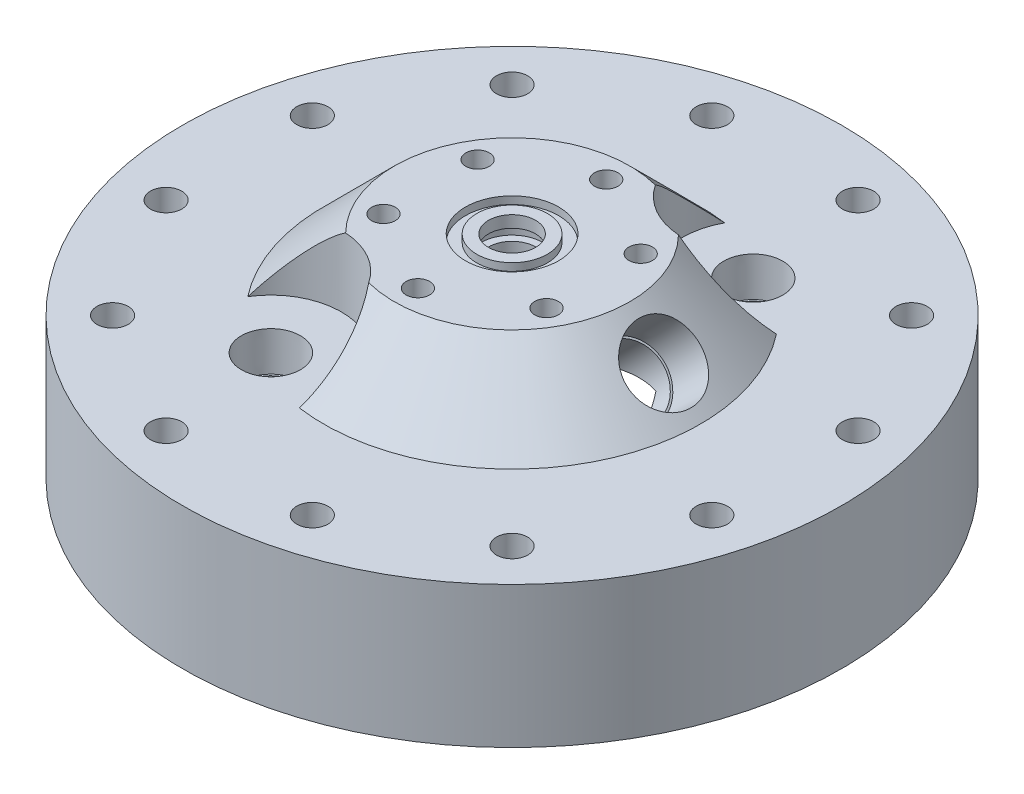
SolidWorks part; units mm, degrees
ref_plane "Front Plane" through (0, 0, 0) normal (0, 0, 1) x (1, 0, 0)
ref_plane "Top Plane" through (0, 0, 0) normal (0, 1, 0) x (1, 0, 0)
ref_plane "Right Plane" through (0, 0, 0) normal (1, 0, 0) x (0, 0, -1)
sketch "Sketch1" plane through (0, 0, 0) normal (0, 0, 1) x (1, 0, 0)
  line L0 (0, 0) -> (0, 51.199) construction
  line L1 (-55.9435, 0) -> (-88.9, 0)
  line L2 (-88.9, 0) -> (-88.9, 38.1)
  line L3 (-88.9, 38.1) -> (-50.8, 38.1)
  line L4 (-50.8, 38.1) -> (-31.75, 57.15)
  line L5 (-31.75, 57.15) -> (-12.573, 57.15)
  line L6 (-6.35, 50.927) -> (-6.35, 31.75)
  line L8 (-31.75, 31.75) -> (-6.35, 31.75)
  line L12 (-31.75, 31.75) -> (-31.75, 19.05)
  line L15 (-31.75, 19.05) -> (-50.8, 19.05)
  line L16 (-50.8, 19.05) -> (-50.8, 0)
  line L17 (-50.8, 0) -> (-52.3875, 0)
  line L18 (-52.3875, 0) -> (-52.3875, 2.54)
  line L19 (-52.3875, 2.54) -> (-55.9435, 2.54)
  line L20 (-55.9435, 2.54) -> (-55.9435, 0)
  line L25 (-6.35, 57.15) -> (-6.35, 53.975)
  line L26 (-6.35, 53.975) -> (-8.382, 53.975)
  line L27 (-8.382, 53.975) -> (-8.382, 50.927)
  line L28 (-8.382, 50.927) -> (-6.35, 50.927)
  line L29 (-12.573, 57.15) -> (-12.573, 55.118)
  line L30 (-12.573, 55.118) -> (-9.525, 55.118)
  line L31 (-9.525, 55.118) -> (-9.525, 57.15)
  line L32 (-9.525, 57.15) -> (-6.35, 57.15)
  dimension "D1" = 6.35
  dimension "D2" = 31.75
  dimension "D3" = 19.05
  dimension "D4" = 25.4
  dimension "D5" = 88.9
  dimension "D6" = 12.7
  dimension "D7" = 135
  dimension "D8" = 6.35
  dimension "D9" = 19.05
  dimension "D10" = 38.1
  dimension "D11" = 3.175
  dimension "D12" = 50.8
  dimension "D13" = 3.556
  dimension "D14" = 2.54
  dimension "D15" = 1.5875
  dimension "D16" = 3.048
  dimension "D17" = 2.032
  dimension "D18" = 3.048
  dimension "D19" = 2.032
  dimension "D20" = 3.175
revolve "Revolve1" add sketch "Sketch1" angle 360 about L0
hole_wizard "5/16 Clearance Hole1" positions "Sketch4" profile "Sketch6" hole size "5/16" standard "ANSI Inch" end condition through all
sketch "Sketch4" plane through (0, 38.1, 0) normal (0, 1, 0) x (1, 0, 0)
  line L0 (-73.6035, -19.722) -> (0, 0) construction
  line L2 (0, 0) -> (-63.9148, 0) construction
  point P0 (-73.6035, -19.722)
  dimension "D1" = 76.2
  dimension "D2" = 15
sketch "Sketch6" plane through (-73.6035, 38.1, 19.722) normal (1, 0, 0) x (0, 0, 1)
  line L0 (0, 0) -> (0, 38.1)
  line L1 (0, 38.1) -> (4.2164, 38.1)
  line L2 (4.2164, 38.1) -> (4.2164, 0)
  line L5 (4.2164, 0) -> (0, 0)
  line L11 (0, -6.35) -> (0, 107.95) construction
  dimension "Thru Hole Dia." = 8.4328
  dimension "Thru Hole Depth" = 38.1
pattern_circular "CirPattern1" count 12 over 360 about axis through (0, 0, 0) along (0, 1, 0) of "5/16 Clearance Hole1"
hole_wizard "1/2 (0.5) Diameter Hole1" positions "Sketch7" profile "Sketch8" hole size "1/2" standard "ANSI Inch" end condition through all
sketch "Sketch7" plane through (0, 57.15, 0) normal (0, 1, 0) x (1, 0, 0)
  point P0 (0, 0)
sketch "Sketch8" plane through (0, 57.15, 0) normal (1, 0, 0) x (0, 0, 1)
  line L0 (0, 0) -> (0, 57.15)
  line L1 (0, 57.15) -> (6.35, 57.15)
  line L2 (6.35, 57.15) -> (6.35, 0)
  line L5 (6.35, 0) -> (0, 0)
  line L11 (0, -6.35) -> (0, 107.95) construction
  dimension "Thru Hole Dia." = 12.7
  dimension "Thru Hole Depth" = 57.15
ref_plane "Plane1" through (44.45, 44.45, 0) normal (0.7071, 0.7071, 0) x (0, 0, -1)
sketch "Sketch9" plane through (44.45, 44.45, 0) normal (0.7071, 0.7071, 0) x (0, 0, -1)
  line L0 (0, -8.9803) -> (0, 17.9605) construction
  ellipse E0 centre (0, 26.9408) end of major axis (-50.8, 26.9408) minor radius 35.921 construction
  ellipse E1 centre (0, 40.4112) end of major axis (-31.75, 40.4112) minor radius 22.4506 construction
  point P15 (0, 4.4901)
hole_wizard "1/2 NPT Tapped Hole1" positions "Sketch10" profile "Sketch11" size "1/2" standard "ANSI Inch" end condition through all
sketch "Sketch10" plane through (44.45, 44.45, 0) normal (0.7071, 0.7071, 0) x (0, 0, -1)
  point P0 (0, 4.4901)
sketch "Sketch11" plane through (41.275, 47.625, 0) normal (0, 0, 1) x (-0.7071, 0.7071, 0)
  line L0 (0, 0) -> (0, 125.7236)
  line L1 (0, 125.7236) -> (8.9281, 125.7236)
  line L2 (-9.4797, 13.462) -> (-9.8828, 0) construction
  line L3 (8.9281, 125.7236) -> (8.9281, 13.462)
  line L4 (8.9281, 13.462) -> (9.4797, 13.462)
  line L5 (9.4797, 13.462) -> (9.8828, 0)
  line L7 (9.8828, 0) -> (0, 0)
  line L8 (0, -6.35) -> (0, 107.95) construction
  line L11 (-8.9281, 13.462) -> (-9.4797, 13.462) construction
  dimension "Thru Tap Drill Dia." = 17.8562
  dimension "Thru Tap Drill Depth" = 125.7236
  dimension "Thread Dia." = 19.7656
  dimension "Thread Angle" = 3.43
  dimension "Thread Depth" = 13.462
cosmetic thread "Hole Thread3" parameters "D1"=13.462, "D2"=36.8399
hole_wizard "1 (1.5) Diameter Hole1" positions "Sketch14" profile "Sketch16" hole size "1" standard "ANSI Inch"
sketch "Sketch14" plane through (0, 57.15, 0) normal (0, 1, 0) x (1, 0, 0)
  line L0 (-23.8125, -41.2445) -> (0, 0) construction
  line L2 (0, 0) -> (-62.2091, 0) construction
  point P0 (-23.8125, -41.2445)
  dimension "D1" = 47.625
  dimension "D2" = 60
sketch "Sketch16" plane through (-23.8125, 57.15, 41.2445) normal (1, 0, 0) x (0, 0, 1)
  line L0 (0, 0) -> (0, 30.4964)
  line L1 (0, 30.4964) -> (19.05, 19.05)
  line L2 (19.05, 19.05) -> (19.05, 0)
  line L5 (19.05, 0) -> (0, 0)
  line L10 (0, 30.4964) -> (-19.05, 19.05) construction
  line L11 (0, -6.35) -> (0, 107.95) construction
  dimension "Hole Dia." = 38.1
  dimension "Hole Depth" = 19.05
  dimension "Drill Angle" = 118
hole_wizard "3/8 NPT Tapped Hole1" positions "Sketch17" profile "Sketch19" size "3/8" standard "ANSI Inch"
sketch "Sketch17" plane through (0, 38.1, 0) normal (0, 1, 0) x (1, 0, 0)
  line L0 (0, 0) -> (-55.2485, 0) construction
  line L2 (0, 0) -> (-23.8125, -41.2445) construction
  point P0 (-23.8125, -41.2445)
  dimension "D1" = 47.625
  dimension "D2" = 60
cosmetic thread "Hole Thread4" parameters "D1"=10.414, "D2"=17.1495
sketch "Sketch19" plane through (-23.8125, 38.1, 41.2445) normal (1, 0, 0) x (0, 0, 1)
  line L0 (0, 0) -> (0, 26.6406)
  line L1 (7.1374, 22.352) -> (0, 26.6406)
  line L2 (-7.1374, 22.352) -> (0, 26.6406) construction
  line L3 (7.1374, 22.352) -> (7.1374, 10.414)
  line L4 (7.1374, 10.414) -> (7.6537, 10.414)
  line L5 (7.6537, 10.414) -> (7.9655, 0)
  line L6 (-7.6537, 10.414) -> (-7.9655, 0) construction
  line L7 (7.9655, 0) -> (0, 0)
  line L8 (0, -6.35) -> (0, 107.95) construction
  line L11 (-7.1374, 10.414) -> (-7.6537, 10.414) construction
  dimension "Tap Drill Dia." = 14.2748
  dimension "Tap Drill Depth" = 22.352
  dimension "Thread Dia." = 15.9311
  dimension "Thread Angle" = 3.43
  dimension "Thread Depth" = 10.414
  dimension "Drill Angle" = 118
hole_wizard "1/4 (0.25) Diameter Hole1" positions "Sketch20" profile "Sketch21" hole size "1/4" standard "ANSI Inch"
sketch "Sketch20" plane through (0, 57.15, 0) normal (0, 1, 0) x (1, 0, 0)
  line L0 (0, 0) -> (21.997, 12.7) construction
  line L2 (0, 0) -> (14.3987, 0) construction
  point P0 (21.997, 12.7)
  dimension "D1" = 25.4
  dimension "D2" = 30
sketch "Sketch21" plane through (21.997, 57.15, -12.7) normal (1, 0, 0) x (0, 0, 1)
  line L0 (0, 0) -> (0, 17.9097)
  line L1 (0, 17.9097) -> (3.175, 16.002)
  line L2 (3.175, 16.002) -> (3.175, 0)
  line L5 (3.175, 0) -> (0, 0)
  line L10 (0, 17.9097) -> (-3.175, 16.002) construction
  line L11 (0, -6.35) -> (0, 107.95) construction
  dimension "Hole Dia." = 6.35
  dimension "Hole Depth" = 16.002
  dimension "Drill Angle" = 118
pattern_circular "CirPattern2" count 6 over 360 about axis through (0, 0, 0) along (0, 1, 0) of "1/4 (0.25) Diameter Hole1"
pattern_circular "CirPattern3" count 2 over 360 about axis through (0, 0, 0) along (0, 1, 0) of "1 (1.5) Diameter Hole1", "3/8 NPT Tapped Hole1"
cosmetic thread "Hole Thread5" parameters "D1"=10.414, "D2"=17.1495
hole_wizard "1/8 (0.125) Diameter Hole1" positions "Sketch22" profile "Sketch23" hole size "1/8" standard "ANSI Inch"
sketch "Sketch22" plane through (0, 19.05, 0) normal (0, -1, 0) x (-1, 0, 0)
  line L0 (0, -44.45) -> (0, 0) construction
  point P0 (0, -44.45)
  dimension "D1" = 44.45
sketch "Sketch23" plane through (0, 19.05, 44.45) normal (1, 0, 0) x (0, 0, -1)
  line L0 (0, 0) -> (0, 7.3039)
  line L1 (0, 7.3039) -> (1.5875, 6.35)
  line L2 (1.5875, 6.35) -> (1.5875, 0)
  line L5 (1.5875, 0) -> (0, 0)
  line L10 (0, 7.3039) -> (-1.5875, 6.35) construction
  line L11 (0, -6.35) -> (0, 107.95) construction
  dimension "Hole Dia." = 3.175
  dimension "Hole Depth" = 6.35
  dimension "Drill Angle" = 118
